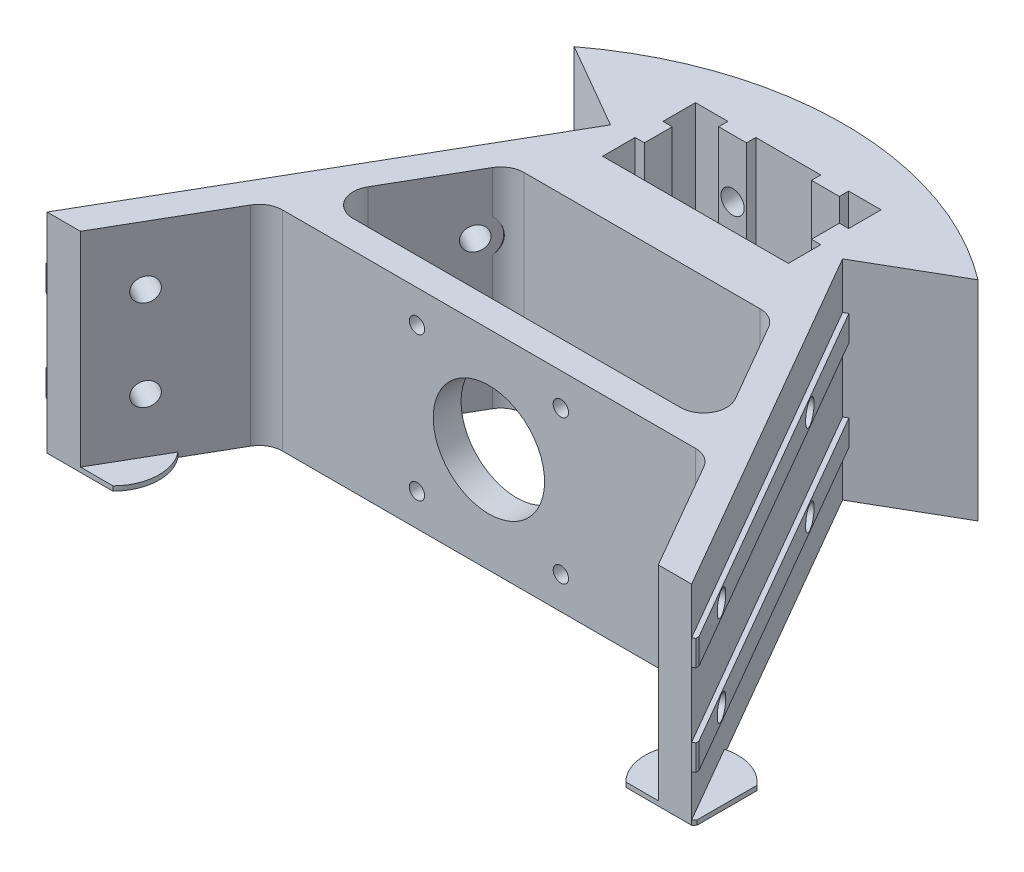
SolidWorks part; units mm, degrees
material "ABS"
ref_plane "Front Plane" through (0, 0, 0) normal (0, 0, 1) x (1, 0, 0)
ref_plane "Top Plane" through (0, 0, 0) normal (0, 1, 0) x (1, 0, 0)
ref_plane "Right Plane" through (0, 0, 0) normal (1, 0, 0) x (0, 0, -1)
sketch "Sketch1" plane through (0, 0, 0) normal (0, 1, 0) x (1, 0, 0)
  line L0 (0, -40) -> (0, 0) construction
  line L1 (-20, 20) -> (-13, 20)
  line L2 (-13, 20) -> (-13, 18)
  line L3 (-13, 18) -> (-7, 18)
  line L4 (-7, 18) -> (-7, 20)
  line L5 (-7, 20) -> (7, 20)
  line L6 (7, 20) -> (7, 18)
  line L7 (7, 18) -> (13, 18)
  line L8 (13, 18) -> (13, 20)
  line L9 (13, 20) -> (20, 20)
  line L10 (20, 20) -> (20, 13)
  line L11 (20, 13) -> (18, 13)
  line L12 (18, 13) -> (18, 7)
  line L13 (18, 7) -> (20, 7)
  line L14 (20, 7) -> (20, 0)
  line L15 (0, 20) -> (0, 0) construction
  line L16 (0, 0) -> (0, 50) construction
  line L17 (0, 50) -> (7.5492, 36.9243) construction
  line L18 (34.641, 70) -> (134.641, -103.2051) construction
  line L19 (20, 0) -> (-20, 0)
  line L20 (0, 50) -> (34.641, 70) construction
  line L21 (134.641, -103.2051) -> (100, -123.2051) construction
  line L22 (67.0736, -66.1749) -> (25, 6.6987)
  line L23 (25, 6.6987) -> (43.4956, 17.3771)
  line L24 (-20, 0) -> (-20, 7)
  line L25 (-20, 7) -> (-18, 7)
  line L26 (-18, 7) -> (-18, 13)
  line L27 (-18, 13) -> (-20, 13)
  line L28 (-20, 13) -> (-20, 20)
  line L29 (59.641, 26.6987) -> (134.641, -103.2051) construction
  line L30 (0, 50) -> (-7.0324, 37.8196) construction
  line L31 (0, 50) -> (-34.641, 70) construction
  line L32 (-34.641, 70) -> (-134.641, -103.2051) construction
  line L33 (-134.641, -103.2051) -> (-59.641, 26.6987) construction
  line L34 (-43.4956, 17.3771) -> (-25, 6.6987)
  line L35 (-25, 6.6987) -> (-67.0736, -66.1749)
  line L36 (-100, -123.2051) -> (-134.641, -103.2051) construction
  line L37 (0, -40) -> (0, -11.5) construction
  line L38 (-25.435, -11.5) -> (25.435, -11.5)
  line L39 (-35.25, -38.5) -> (35.25, -38.5)
  line L40 (-29.7652, -14) -> (-39.5801, -31)
  line L41 (29.7652, -14) -> (39.5801, -31)
  line L42 (-39.5801, -31) -> (-44.9691, -27.8887) construction
  line L43 (-39.5801, -31) -> (-47.1202, -44.0598) construction
  line L44 (-29.7652, -14) -> (-43.2264, -37.3156) construction
  line L45 (-35.1541, -10.8887) -> (-29.7652, -14) construction
  line L46 (-48.8177, -47) -> (-63.915, -73.1492)
  line L47 (-44.4876, -44.5) -> (44.4876, -44.5)
  line L48 (29.7652, -14) -> (39.5801, -31) construction
  line L49 (39.5801, -31) -> (46.43, -42.8643) construction
  line L50 (48.8177, -47) -> (63.915, -73.1492)
  line L51 (-67.0736, -66.1749) -> (-71.1002, -73.1492)
  line L52 (-71.1002, -73.1492) -> (-63.915, -73.1492)
  line L53 (67.0736, -66.1749) -> (71.1002, -73.1492)
  line L54 (71.1002, -73.1492) -> (63.915, -73.1492)
  arc A0 (63.915, -73.1492) -> (67.0736, -66.1749) centre (0, -40) ccw construction
  arc A1 (-25.435, -11.5) -> (-29.7652, -14) centre (-25.435, -16.5) ccw
  arc A2 (29.7652, -14) -> (25.435, -11.5) centre (25.435, -16.5) ccw
  arc A3 (35.25, -38.5) -> (39.5801, -31) centre (35.25, -33.5) ccw
  arc A4 (-39.5801, -31) -> (-35.25, -38.5) centre (-35.25, -33.5) ccw
  arc A5 (-44.4876, -44.5) -> (-48.8177, -47) centre (-44.4876, -49.5) ccw
  arc A6 (48.8177, -47) -> (44.4876, -44.5) centre (44.4876, -49.5) ccw
  arc A7 (-67.0736, -66.1749) -> (-63.915, -73.1492) centre (0, -40) ccw construction
  arc A8 (43.4956, 17.3771) -> (-43.4956, 17.3771) centre (0, -40) ccw
  dimension "D1" = 144
  dimension "D14" = 10
  dimension "D2" = 40
  dimension "D3" = 6
  dimension "D4" = 2
  dimension "D5" = 40
  dimension "D6" = 20
  dimension "D7" = 50
  dimension "D8" = 30
  dimension "D9" = 40
  dimension "D10" = 200
  dimension "D11" = 150
  dimension "D12" = 30
  dimension "D13" = 1.5
  dimension "D15" = 17
  dimension "D17" = 70.5
  dimension "D18" = 6
extrude "Boss-Extrude1" add sketch "Sketch1" along normal blind 45
sketch "Sketch2" plane through (0, 0, 44.5) normal (0, 0, 1) x (1, 0, 0)
  line L0 (0, 45) -> (0, 0) construction
  line L1 (-44.4876, 45) -> (44.4876, 45) construction
  line L2 (-15.5, 38) -> (0, 22.5) construction
  line L3 (0, 22.5) -> (15.5, 38) construction
  line L4 (0, 22.5) -> (15.5, 7) construction
  line L5 (-15.5, 7) -> (0, 22.5) construction
  circle A0 centre (0, 22.5) radius 12
  circle A1 centre (-15.5, 38) radius 1.65
  circle A2 centre (15.5, 38) radius 1.65
  circle A3 centre (15.5, 7) radius 1.65
  circle A4 centre (-15.5, 7) radius 1.65
  dimension "D1" = 24
  dimension "D2" = 3.3
  dimension "D3" = 31
  dimension "D4" = 31
extrude "Cut-Extrude1" cut sketch "Sketch2" against normal up to next
sketch "Sketch3" plane through (21.6506, 0, -12.5) normal (0.866, 0, -0.5) x (-0.5, 0, -0.866)
  line L0 (-98.8992, 35) -> (-6.6987, 35)
  line L1 (-98.8992, 45) -> (-98.8992, 0) construction
  line L2 (-6.6987, 45) -> (-6.6987, 0) construction
  line L3 (-6.6987, 35) -> (-6.6987, 29.5)
  line L4 (-6.6987, 29.5) -> (-98.8992, 29.5)
  line L5 (-98.8992, 29.5) -> (-98.8992, 35)
  line L6 (-98.8992, 15.5) -> (-6.6987, 15.5)
  line L7 (-6.6987, 15.5) -> (-6.6987, 10)
  line L8 (-6.6987, 10) -> (-98.8992, 10)
  line L9 (-98.8992, 10) -> (-98.8992, 15.5)
  line L10 (-98.8992, 22.5) -> (-6.6987, 22.5) construction
  line L11 (-6.6987, 45) -> (-6.6987, 0) construction
  line L12 (-98.8992, 22.5) -> (-98.8992, 29.5) construction
  line L13 (-98.8992, 22.5) -> (-98.8992, 15.5) construction
  dimension "D1" = 5.5
  dimension "D2" = 7
extrude "Boss-Extrude2" add sketch "Sketch3" along normal blind 1
sketch "Sketch4" plane through (22.5167, 0, -13) normal (0.866, 0, -0.5) x (-0.5, 0, -0.866)
  line L0 (-6.6987, 32.25) -> (-98.8992, 32.25) construction
  line L1 (-6.6987, 29.5) -> (-6.6987, 35) construction
  line L2 (-98.8992, 35) -> (-98.8992, 29.5) construction
  line L3 (-98.8992, 12.75) -> (-6.6987, 12.75) construction
  line L4 (-98.8992, 15.5) -> (-98.8992, 10) construction
  line L5 (-6.6987, 10) -> (-6.6987, 15.5) construction
  line L6 (-6.6987, 45) -> (-6.6987, 0) construction
  circle A0 centre (-29.6987, 32.25) radius 2.5
  circle A1 centre (-29.6987, 12.75) radius 2.5
  circle A2 centre (-81.6987, 12.75) radius 2.5
  circle A3 centre (-81.6987, 32.25) radius 2.5
  dimension "D1" = 5
  dimension "D3" = 75
  dimension "D2" = 23
extrude "Cut-Extrude2" cut sketch "Sketch4" against normal up to next
sketch "Sketch7" plane through (16.2617, 0, -9.3887) normal (-0.866, 0, 0.5) x (0.5, 0, 0.866)
  circle A0 centre (29.6987, 32.25) radius 4.5
  circle A1 centre (29.6987, 12.75) radius 4.5
  dimension "D1" = 9
extrude "Cut-Extrude6" cut sketch "Sketch7" along normal up to next
sketch "Sketch5" plane through (0, 0, -18) normal (0, 0, 1) x (1, 0, 0)
  line L0 (7, 22.5) -> (13, 22.5) construction
  line L1 (7, 45) -> (7, 0) construction
  line L2 (13, 45) -> (13, 0) construction
  line L3 (10, 22.5) -> (10, 32.5) construction
  line L4 (10, 22.5) -> (10, 12.5) construction
  circle A0 centre (10, 32.5) radius 2.5
  circle A1 centre (10, 12.5) radius 2.5
  dimension "D1" = 20
  dimension "D2" = 5
extrude "Cut-Extrude3" cut sketch "Sketch5" against normal up to next
sketch "Sketch6" plane through (0, 0, -18) normal (0, 0, 1) x (1, 0, 0)
  circle A0 centre (10, 32.5) radius 4.25
  circle A1 centre (10, 12.5) radius 4.25
  dimension "D1" = 8.5
extrude "Cut-Extrude5" cut sketch "Sketch6" along normal blind 1.7 from offset 14 offset against normal yes
mirror "Mirror1" about plane through (0, 0, 0) normal (1, 0, 0) of "Cut-Extrude6", "Cut-Extrude5", "Cut-Extrude3", "Cut-Extrude2", "Boss-Extrude2"
sketch "Sketch8" plane through (0, 0, 0) normal (0, 1, 0) x (1, 0, 0)
  line L0 (59.2113, -65.0022) -> (65.4663, -61.3909) construction
  line L1 (48.8177, -47) -> (63.915, -73.1492) construction
  line L2 (25.866, 7.1987) -> (71.9663, -72.6492) construction
  line L3 (71.9663, -72.6492) -> (71.1002, -73.1492) construction
  line L4 (-59.2113, -65.0022) -> (-65.4663, -61.3909) construction
  line L5 (-63.915, -73.1492) -> (-48.8177, -47) construction
  line L6 (-25.866, 7.1987) -> (-71.9663, -72.6492) construction
  circle A0 centre (62.3388, -63.1966) radius 10
  circle A1 centre (-62.3388, -63.1966) radius 10
  dimension "D1" = 20
  dimension "D2" = 13
extrude "Boss-Extrude3" add sketch "Sketch8" along normal blind 1
sketch "Sketch10" plane through (49.4496, 0, 85.6492) normal (0.5, 0, 0.866) x (0.866, 0, -0.5)
  line L1 (25, 29.5) -> (26, 29.5)
  line L2 (26, 29.5) -> (25, 27.3555)
  line L3 (25, 29.5) -> (25, 15.5) construction
  line L4 (25, 27.3555) -> (25, 29.5)
  line L5 (25, 10) -> (26, 10)
  line L6 (26, 10) -> (25, 7.8555)
  line L7 (25, 10) -> (25, 0) construction
  line L8 (25, 7.8555) -> (25, 10)
  dimension "D1" = 65
extrude "Boss-Extrude4" [suppressed] add sketch "Sketch10" against normal blind 0.7
pattern_linear "LPattern1" [suppressed] count 46 spacing 2
sketch "Sketch11" plane through (-49.4496, 0, 85.6492) normal (-0.5, 0, 0.866) x (0.866, 0, 0.5)
  line L0 (-25, 29.5) -> (-26, 29.5)
  line L1 (-26, 29.5) -> (-25, 27.3555)
  line L2 (-25, 29.5) -> (-25, 15.5) construction
  line L3 (-25, 27.3555) -> (-25, 29.5)
  line L4 (-25, 10) -> (-26, 10)
  line L5 (-26, 10) -> (-25, 7.8555)
  line L6 (-25, 10) -> (-25, 0) construction
  line L7 (-25, 7.8555) -> (-25, 10)
  dimension "D1" = 65
extrude "Boss-Extrude5" [suppressed] add sketch "Sketch11" against normal blind 0.7
pattern_linear "LPattern2" [suppressed] count 46 spacing 2
sketch "Sketch12" plane through (0, 0, 0) normal (0, 1, 0) x (1, 0, 0)
  line L0 (80, -70.2492) -> (80, -53.1492)
  line L1 (-80, -75.1492) -> (80, -75.1492)
  line L2 (-80, -75.1492) -> (-80, -70.2492)
  line L3 (-69.4259, -70.2492) -> (69.4259, -70.2492)
  line L4 (80, -75.1492) -> (80, -70.2492)
  line L5 (80, -53.1492) -> (70, -53.1492)
  line L6 (70, -53.1492) -> (70, -69.9178)
  line L7 (71.1002, -73.1492) -> (25, 6.6987) construction
  line L8 (-80, -70.2492) -> (-80, -53.1492)
  line L9 (-80, -53.1492) -> (-70, -53.1492)
  line L10 (-70, -53.1492) -> (-70, -69.9178)
  line L11 (-25, 6.6987) -> (-71.1002, -73.1492) construction
  line L12 (69.4259, -70.2492) -> (70, -69.9178)
  line L13 (-69.4259, -70.2492) -> (-70, -69.9178)
  line L14 (-25, 6.6987) -> (-71.1002, -73.1492) construction
  line L15 (-71.1002, -73.1492) -> (-63.915, -73.1492) construction
  dimension "D1" = 80
  dimension "D2" = 160
  dimension "D3" = 4.9
  dimension "D4" = 22
  dimension "D5" = 2
  dimension "D7" = 10
extrude "Cut-Extrude7" cut sketch "Sketch12" along normal through all
equation "\"D12@Sketch1\"=\"D8@Sketch1\""
equation "\"D4@Sketch2\"=\"D3@Sketch2\""
equation "\"D2@Sketch3\"=(20-6)/2"
